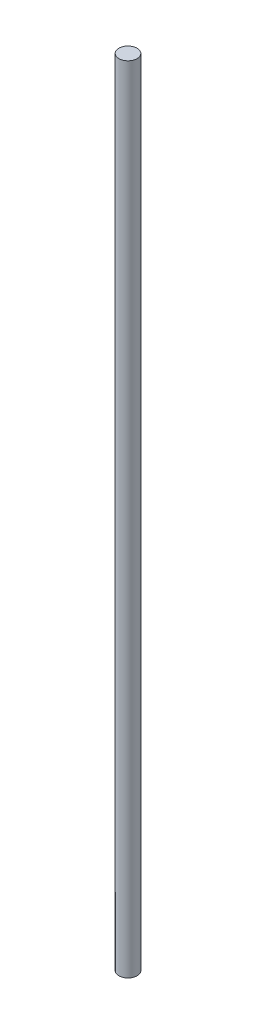
SolidWorks part; units mm, degrees
ref_plane "前基準面" through (0, 0, 0) normal (0, 0, 1) x (1, 0, 0)
ref_plane "上基準面" through (0, 0, 0) normal (0, 1, 0) x (1, 0, 0)
ref_plane "右基準面" through (0, 0, 0) normal (1, 0, 0) x (0, 0, -1)
sketch "草圖1" plane through (0, 0, 0) normal (0, 1, 0) x (1, 0, 0)
  circle A0 centre (0, 0) radius 4
  dimension "D1" = 8
extrude "填料-伸長1" add sketch "草圖1" along normal blind 350
